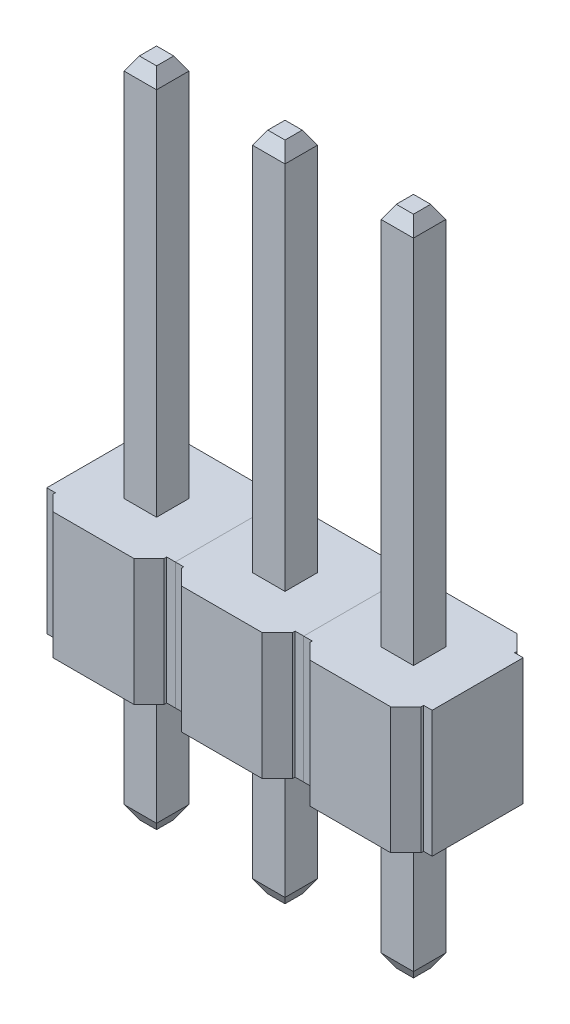
SolidWorks part; units mm, degrees
ref_plane "Front" through (0, 0, 0) normal (0, 0, 1) x (1, 0, 0)
ref_plane "Top" through (0, 0, 0) normal (0, 1, 0) x (1, 0, 0)
ref_plane "Right" through (0, 0, 0) normal (1, 0, 0) x (0, 0, -1)
sketch "HEADER PATH" plane through (0, 0, 0) normal (1, 0, 0) x (0, 0, -1)
  line L0 (0, 0) -> (0, -3)
  line L1 (0, 0) -> (0, 10.08)
  point P4 (0.7141, 4.08)
  point P5 (0, 4.2333)
  point P6 (0, 3.8546)
  point P7 (0, 10.08)
  point P8 (0, 0)
  point P9 (0, 0)
  point P10 (0, 8.4665)
  point P11 (0, 8.16)
  point P12 (0, 4.08)
  dimension "D1" = 3
  dimension "D2" = 10.08
sketch "HEADER PROFILE" plane through (0, 0, 0) normal (0, 1, 0) x (1, 0, 0)
  line L1 (-0.32, -0.32) -> (0.32, -0.32)
  line L2 (-0.32, -0.32) -> (-0.32, 0.32)
  line L3 (-0.32, 0.32) -> (0.32, 0.32)
  line L4 (0.32, -0.32) -> (0.32, 0.32)
  line L5 (-0.32, -0.32) -> (0.32, 0.32) construction
  line L6 (-0.32, 0.32) -> (0.32, -0.32) construction
  point P0 (0, 0)
  dimension "D1" = 0.64
sweep "PIN PROFILE" add profiles "HEADER PROFILE" path "HEADER PATH"
chamfer "END PIN PROFILE" distance 0.15 angle 60 8 edges at (0, -3, -0.32) (-0.32, -3, 0) (0, -3, 0.32) (0.32, -3, 0) (0, 10.08, 0.32) (-0.32, 10.08, 0) (0, 10.08, -0.32) (0.32, 10.08, 0)
sketch "Эскиз4" plane through (0, 0, 0) normal (0, 1, 0) x (1, 0, 0)
  line L0 (-1.1, 0.9) -> (-1.1, 1.25)
  line L1 (-1.1, -1.25) -> (1.1, -1.25)
  line L2 (-1.1, -1.25) -> (-1.1, -0.9)
  line L3 (-1.1, 1.25) -> (1.1, 1.25)
  line L4 (1.1, -1.25) -> (1.1, -0.9)
  line L5 (-1.1, -1.25) -> (1.1, 1.25) construction
  line L6 (-1.1, 1.25) -> (1.1, -1.25) construction
  line L7 (-1.27, -0.9) -> (-1.1, -0.9)
  line L8 (-1.27, -0.9) -> (-1.27, 0.9)
  line L9 (-1.27, 0.9) -> (-1.1, 0.9)
  line L10 (1.27, -0.9) -> (1.27, 0.9)
  line L11 (-1.27, -0.9) -> (1.27, 0.9) construction
  line L12 (-1.27, 0.9) -> (1.27, -0.9) construction
  line L13 (1.1, 0.9) -> (1.1, 1.25)
  line L14 (1.1, -0.9) -> (1.27, -0.9)
  line L15 (1.1, 0.9) -> (1.27, 0.9)
  point P0 (0, 0)
  point P5 (0, 0)
  dimension "D1" = 2.2
  dimension "D2" = 2.5
  dimension "D3" = 1.8
  dimension "D4" = 2.54
extrude "BASE BODY" add sketch "Эскиз4" along normal blind 2.5 separate body
chamfer "BB CHAMFER" distance 0.3 angle 45 4 edges at (-1.1, 1.25, -1.25) (1.1, 1.25, -1.25) (-1.1, 1.25, 1.25) (1.1, 1.25, 1.25)
pattern_linear "LP ALL" count 2 spacing 2.54 along (-1, 0, 0) count 2 spacing 2.54 along (1, 0, 0) of bodies 102 101
equation "\"D2@HEADER PATH\"=10.4 - 0.64 / 2"
